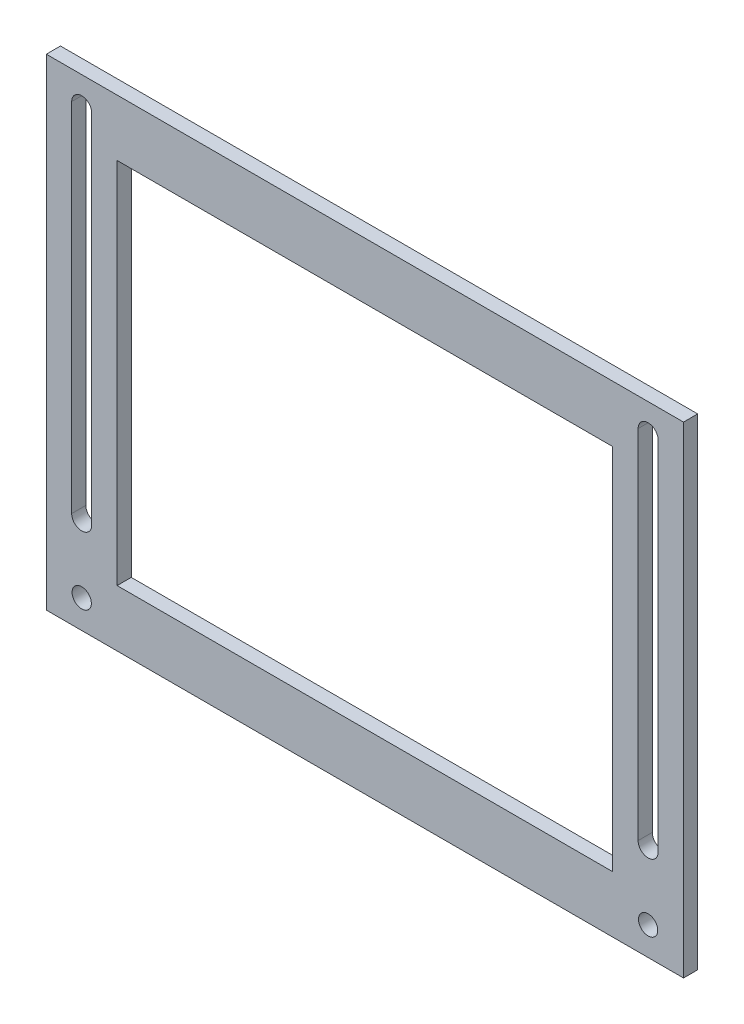
SolidWorks part; units mm, degrees
ref_plane "Front" through (0, 0, 0) normal (0, 0, 1) x (1, 0, 0)
ref_plane "Top" through (0, 0, 0) normal (0, 1, 0) x (1, 0, 0)
ref_plane "Right" through (0, 0, 0) normal (1, 0, 0) x (0, 0, -1)
sketch "Sketch1" plane through (0, 0, 0) normal (0, 0, 1) x (1, 0, 0)
  line L0 (7.9375, 101.6) -> (7.9375, 21.59) construction
  line L1 (0, 0) -> (15.875, 0)
  line L2 (0, 0) -> (0, 107.95)
  line L3 (0, 107.95) -> (15.875, 107.95)
  line L7 (7.9375, 0) -> (7.9375, 101.6) construction
  line L8 (10.1854, 101.6) -> (10.1854, 21.59)
  line L9 (5.6896, 101.6) -> (5.6896, 21.59)
  line L10 (7.9375, 6.35) -> (71.4375, 6.35) construction
  line L11 (71.4375, -29.9281) -> (71.4375, 129.3633) construction
  line L12 (15.875, 12.7) -> (15.875, 95.25)
  line L21 (15.875, 107.95) -> (127, 107.95)
  line L22 (15.875, 95.25) -> (127, 95.25)
  line L23 (15.875, 12.7) -> (127, 12.7)
  line L24 (15.875, 0) -> (127, 0)
  line L25 (134.9375, 0) -> (134.9375, 101.6) construction
  line L26 (127, 12.7) -> (127, 95.25)
  line L27 (142.875, 107.95) -> (127, 107.95)
  line L28 (142.875, 0) -> (142.875, 107.95)
  line L29 (142.875, 0) -> (127, 0)
  line L30 (134.9375, 101.6) -> (134.9375, 21.59) construction
  line L31 (132.6896, 101.6) -> (132.6896, 21.59)
  line L32 (137.1854, 101.6) -> (137.1854, 21.59)
  circle A2 centre (7.9375, 6.35) radius 2.159
  arc A3 (10.1854, 101.6) -> (5.6896, 101.6) centre (7.9375, 101.6) ccw
  arc A4 (5.6896, 21.59) -> (10.1854, 21.59) centre (7.9375, 21.59) ccw
  circle A5 centre (134.9375, 6.35) radius 2.159
  arc A6 (132.6896, 101.6) -> (137.1854, 101.6) centre (134.9375, 101.6) cw
  arc A7 (137.1854, 21.59) -> (132.6896, 21.59) centre (134.9375, 21.59) cw
  point P7 (7.9375, 61.595)
  point P30 (71.4375, 0)
  point P31 (71.4375, 12.7)
  point P32 (71.4375, 95.25)
  point P33 (71.4375, 107.95)
  point P36 (134.9375, 61.595)
  dimension "D3" = 4.318
  dimension "D4" = 2.2479
  dimension "D1" = 107.95
  dimension "D2" = 15.875
  dimension "D5" = 15.24
  dimension "D6" = 6.35
  dimension "D7" = 6.35
  dimension "D8" = 63.5
  dimension "D9" = 12.7
  dimension "D10" = 12.7
extrude "Boss-Extrude1" add sketch "Sketch1" along normal blind 3.175
